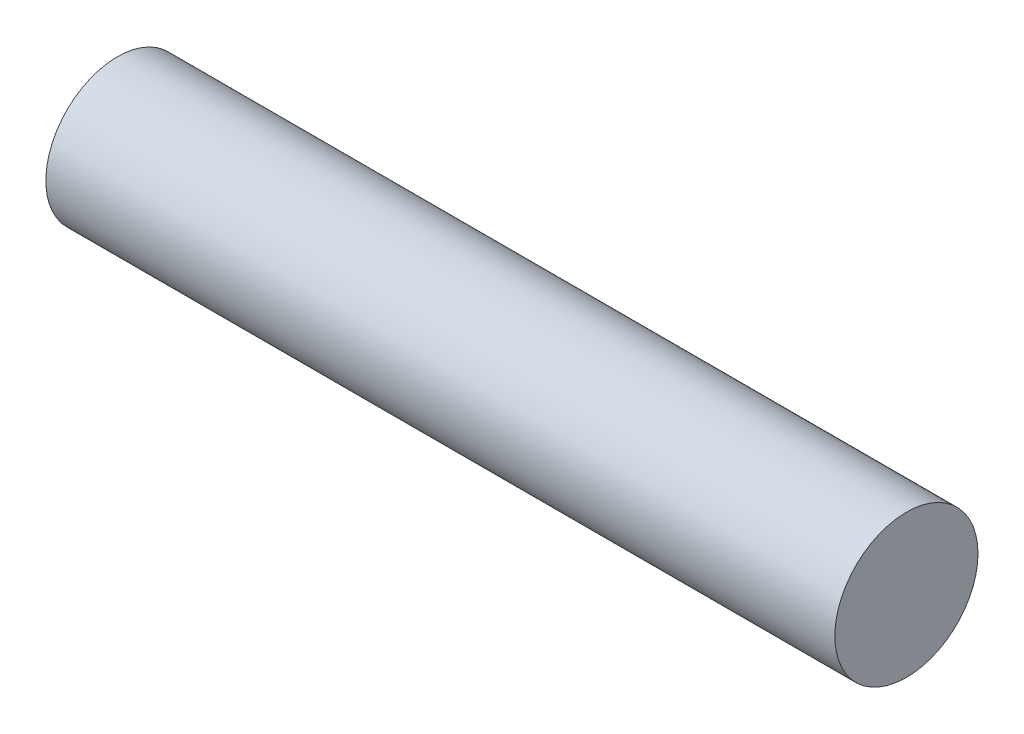
SolidWorks part; units mm, degrees
ref_plane "Plan de face" through (0, 0, 0) normal (0, 0, 1) x (1, 0, 0)
ref_plane "Plan de dessus" through (0, 0, 0) normal (0, 1, 0) x (1, 0, 0)
ref_plane "Plan de droite" through (0, 0, 0) normal (1, 0, 0) x (0, 0, -1)
sketch "Esquisse1" plane through (0, 0, 0) normal (1, 0, 0) x (0, 0, -1)
  circle A0 centre (0, 0) radius 4.9
  dimension "D1" = 9.8
extrude "Boss.-Extru.1" add sketch "Esquisse1" along normal mid plane 54
